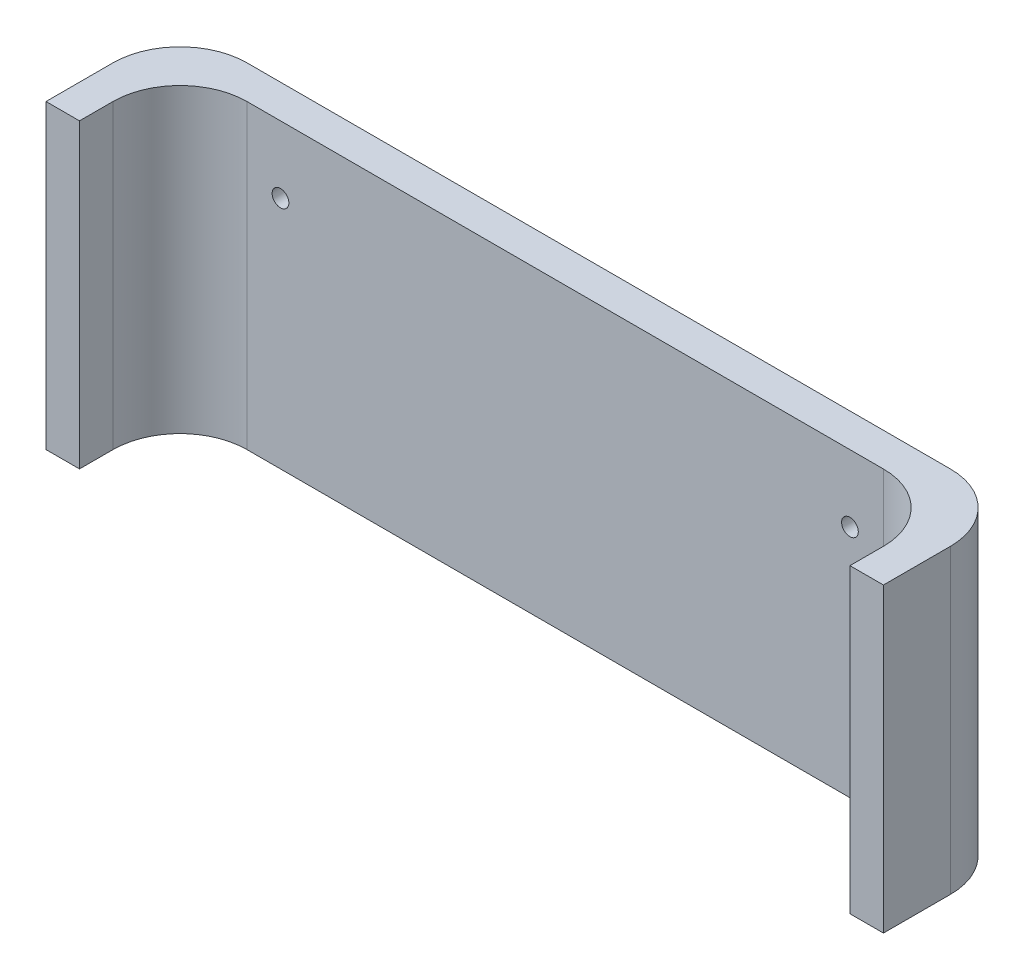
SolidWorks part; units mm, degrees
ref_plane "Front Plane" through (0, 0, 0) normal (0, 0, 1) x (1, 0, 0)
ref_plane "Top Plane" through (0, 0, 0) normal (0, 1, 0) x (1, 0, 0)
ref_plane "Right Plane" through (0, 0, 0) normal (1, 0, 0) x (0, 0, -1)
sketch "Sketch1" plane through (0, 0, 0) normal (0, 1, 0) x (1, 0, 0)
  line L1 (-125, -125) -> (125, -125)
  line L2 (-125, -125) -> (-125, 125)
  line L3 (-125, 125) -> (125, 125)
  line L4 (125, -125) -> (125, 125)
  line L5 (-115, -115) -> (115, -115)
  line L6 (-115, -115) -> (-115, 115)
  line L7 (-115, 115) -> (115, 115)
  line L8 (115, -115) -> (115, 115)
  line L9 (-115, -115) -> (115, 115) construction
  line L10 (-115, 115) -> (115, -115) construction
  point P0 (0, 0)
  point P6 (125, 0)
  point P7 (0, -125)
  point P8 (0, 0)
  dimension "D1" = 250
  dimension "D2" = 250
  dimension "D3" = 230
  dimension "D4" = 230
extrude "Boss-Extrude1" add sketch "Sketch1" along normal blind 90
sketch "Sketch2" plane through (0, 0, 125) normal (0, 0, 1) x (1, 0, 0)
  line L0 (-125, 0) -> (125, 0) construction
  line L1 (-100, 70) -> (100, 70)
  line L2 (-100, 70) -> (-100, 0)
  line L3 (-100, 0) -> (100, 0)
  line L4 (100, 70) -> (100, 0)
  line L6 (-125, 90) -> (125, 90) construction
  point P6 (0, 70)
  dimension "D1" = 200
  dimension "D2" = 20
extrude "Cut-Extrude1" cut sketch "Sketch2" against normal blind 50
fillet "Fillet1" radius 20 8 edges at (-115, 45, 115) (115, 45, 115) (115, 45, -115) (-115, 45, -115) (-125, 45, 125) (125, 45, 125) (125, 45, -125) (-125, 45, -125)
sketch "Sketch3" plane through (-125, 0, 0) normal (-1, 0, 0) x (0, 0, 1)
  line L0 (-105, 90) -> (105, 90) construction
  line L1 (-85, 90) -> (125, 90)
  line L2 (-85, 90) -> (-85, 0)
  line L3 (-85, 0) -> (125, 0)
  line L4 (125, 90) -> (125, 0)
  dimension "D1" = 210
extrude "Cut-Extrude2" cut sketch "Sketch3" against normal through all
sketch "Sketch4" plane through (0, 0, -125) normal (0, 0, -1) x (-1, 0, 0)
  line L0 (-105, 90) -> (105, 90) construction
  line L1 (105, 0) -> (105, 90) construction
  line L2 (-105, 90) -> (-105, 0) construction
  circle A0 centre (85, 70) radius 2.5
  circle A1 centre (-85, 70) radius 2.5
  dimension "D3" = 5
  dimension "D4" = 5
  dimension "D1" = 20
  dimension "D2" = 20
  dimension "D5" = 20
  dimension "D6" = 20
extrude "Cut-Extrude3" cut sketch "Sketch4" against normal blind 10
